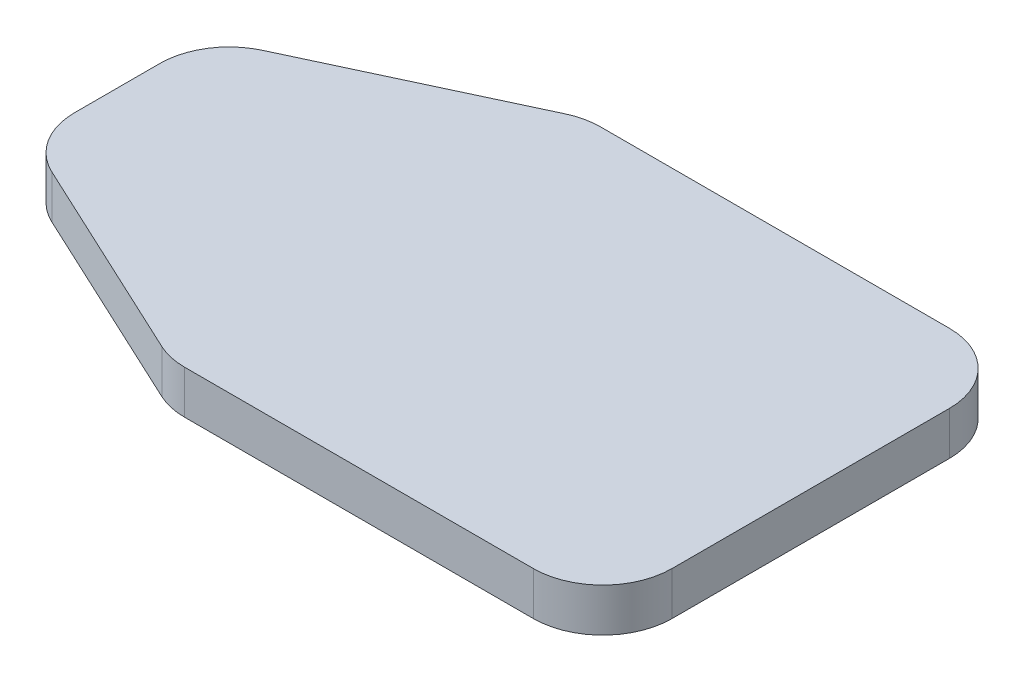
SolidWorks part; units mm, degrees
ref_plane "Front Plane" through (0, 0, 0) normal (0, 0, 1) x (1, 0, 0)
ref_plane "Top Plane" through (0, 0, 0) normal (0, 1, 0) x (1, 0, 0)
ref_plane "Right Plane" through (0, 0, 0) normal (1, 0, 0) x (0, 0, -1)
sketch "Sketch1" plane through (0, 0, 0) normal (0, 1, 0) x (1, 0, 0)
  line L0 (-25.4, 6.35) -> (-6.35, 15.24)
  line L1 (-25.4, 15.24) -> (25.4, 15.24)
  line L2 (-25.4, 15.24) -> (-25.4, -15.24)
  line L3 (-25.4, -15.24) -> (25.4, -15.24)
  line L4 (25.4, 15.24) -> (25.4, -15.24)
  line L5 (-25.4, -6.35) -> (-6.35, -15.24)
  point P4 (0, 15.24)
  point P5 (-25.4, 0)
  dimension "D1" = 30.48
  dimension "D2" = 50.8
  dimension "D3" = 19.05
  dimension "D4" = 8.89
extrude "Boss-Extrude1" add sketch "Sketch1" along normal blind 3.175 contours L2 L5 L3 L4 L1 L0
fillet "Fillet2" radius 5.08 6 edges at (25.4, 1.5875, 15.24) (25.4, 1.5875, -15.24) (-6.35, 1.5875, -15.24) (-25.4, 1.5875, -6.35) (-25.4, 1.5875, 6.35) (-6.35, 1.5875, 15.24)
move or copy body "Body-Move/Copy1" [suppressed] bodies to move or copy 101 parameters "D1"=0, "D2"=0, "D3"=0
